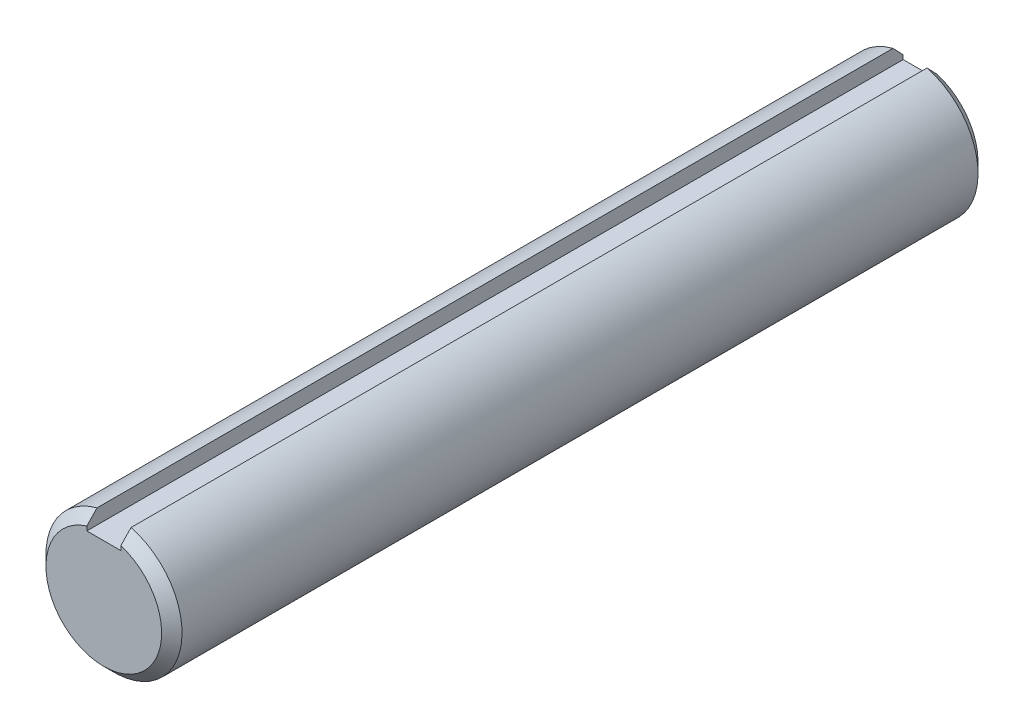
SolidWorks part; units mm, degrees
ref_plane "Front" through (0, 0, 0) normal (0, 0, 1) x (1, 0, 0)
ref_plane "Top" through (0, 0, 0) normal (0, 1, 0) x (1, 0, 0)
ref_plane "Right" through (0, 0, 0) normal (1, 0, 0) x (0, 0, -1)
sketch "Sketch1" plane through (0, 0, 0) normal (0, 0, 1) x (1, 0, 0)
  circle A0 centre (0, 0) radius 6.35
  dimension "dia" = 12.7
extrude "Extrude1" add sketch "Sketch1" along normal mid plane 76.2
sketch "Sketch2" plane through (0, 0, 0) normal (1, 0, 0) x (0, 0, -1)
  point P0 (-38.1, 6.35)
  point P1 (38.1, 6.35)
  point P2 (38.1, -6.35)
chamfer "Chamfer1" distance 0.9525 angle 45 2 edges at (6.35, 0, -38.1) (6.35, 0, 38.1)
sketch "Sketch3" plane through (0, 0, 0) normal (0, 0, 1) x (1, 0, 0)
  line L1 (-1.5875, 6.35) -> (1.5875, 6.35)
  line L2 (-1.5875, 6.35) -> (-1.5875, 4.7625)
  line L3 (-1.5875, 4.7625) -> (1.5875, 4.7625)
  line L4 (1.5875, 6.35) -> (1.5875, 4.7625)
  dimension "key wd" = 3.175
  dimension "key dp" = 1.5875
extrude "Extrude2" cut sketch "Sketch3" against normal through all and the other way through all
equation "\"D1@Chamfer1\" = \"dia@Sketch1\" * .075"
